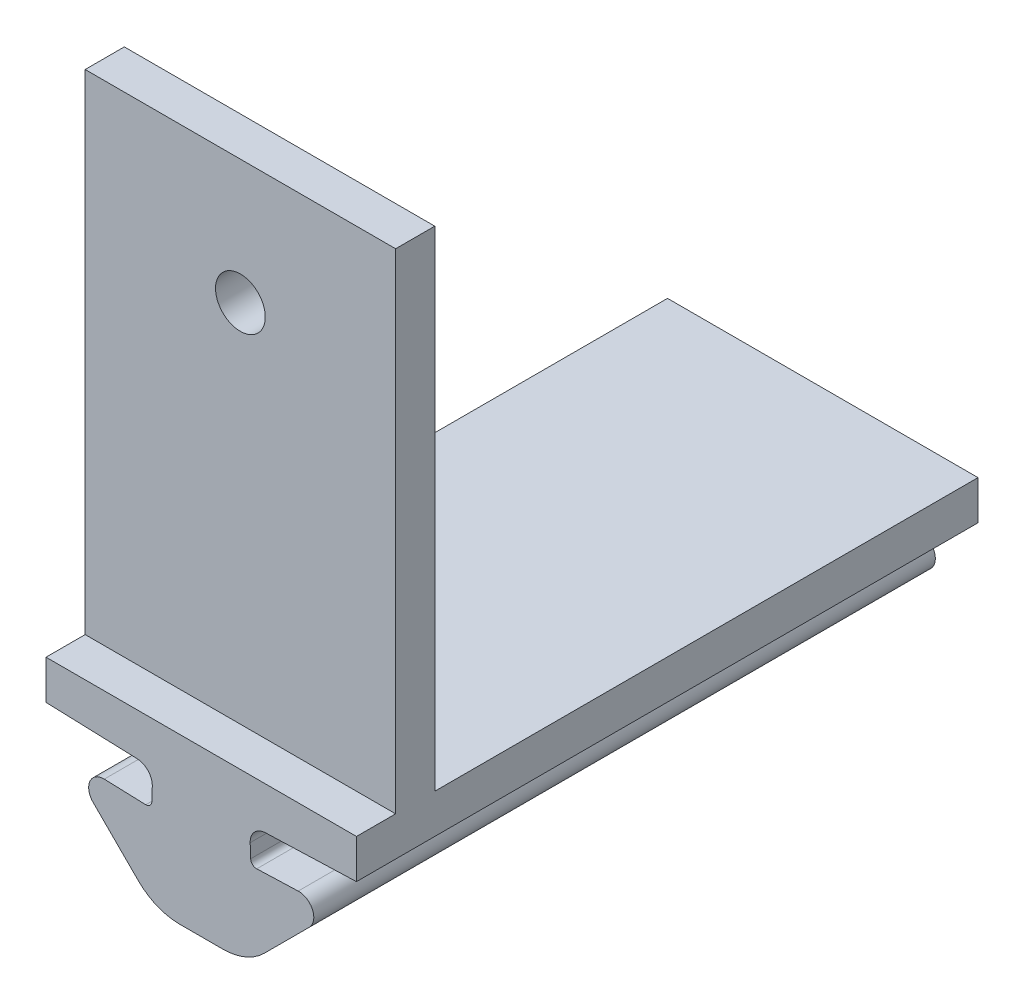
SolidWorks part; units mm, degrees
ref_plane "Front Plane" through (0, 0, 0) normal (0, 0, 1) x (1, 0, 0)
ref_plane "Top Plane" through (0, 0, 0) normal (0, 1, 0) x (1, 0, 0)
ref_plane "Right Plane" through (0, 0, 0) normal (1, 0, 0) x (0, 0, -1)
sketch "Sketch2" plane through (0, 0, 0) normal (0, 0, 1) x (1, 0, 0)
  line L1 (-50.3756, 45.6099) -> (-50.3512, 46.3094)
  line L2 (-50.6859, 45.3205) -> (-52.8037, 45.3945)
  line L6 (-55.7809, 47.2995) -> (-51.1228, 47.1369)
  line L7 (-51.0743, 41.7794) -> (-53.3751, 44.0803)
  line L8 (-47.8507, 40.9008) -> (-48.9529, 40.9008)
  line L9 (-47.8507, 40.9008) -> (-47.8507, 47.2995)
  line L10 (-47.8507, 47.2995) -> (-55.7809, 47.2995)
  arc A0 (-50.6859, 45.3205) -> (-50.3756, 45.6099) centre (-50.6754, 45.6203) ccw
  arc A7 (-50.3512, 46.3094) -> (-51.1228, 47.1369) centre (-51.1507, 46.3374) ccw
  arc A8 (-52.8037, 45.3945) -> (-53.3751, 44.0803) centre (-52.8306, 44.6248) ccw
  arc A9 (-51.0743, 41.7794) -> (-48.9529, 40.9008) centre (-48.9529, 43.9008) ccw
extrude "Boss-Extrude1" add sketch "Sketch2" along normal blind 31.75
ref_plane "Plane2" through (0, 0, 0) normal (0.7071, -0.7071, 0) x (-0.7071, -0.7071, 0)
ref_plane "Plane3" through (-42.746, 42.746, 0) normal (0.7071, -0.7071, 0) x (-0.7071, -0.7071, 0)
mirror "Mirror2" about plane through (-47.8507, 40.9008, 31.75) normal (-1, 0, 0) of "Boss-Extrude1"
ref_plane "Plane7" through (0, 47.2995, 0) normal (0, 1, 0) x (1, 0, 0)
sketch "Sketch19" plane through (0, 47.2995, 0) normal (0, 1, 0) x (1, 0, 0)
  line L0 (-55.7809, -31.75) -> (-55.7809, 0) construction
  line L1 (-55.7809, 0) -> (-39.9205, 0)
  line L2 (-55.7809, 0) -> (-55.7809, -31.75)
  line L3 (-55.7809, -31.75) -> (-39.9205, -31.75)
  line L4 (-39.9205, 0) -> (-39.9205, -31.75)
  line L5 (-39.9205, -31.75) -> (-39.9205, 0) construction
  line L6 (-39.9205, 0) -> (-55.7809, 0) construction
  dimension "D1" = 0
  dimension "D2" = 31.75
extrude "Boss-Extrude7" add sketch "Sketch19" along normal blind 2
sketch "Sketch23" plane through (0, 49.2995, 0) normal (0, 1, 0) x (1, 0, 0)
  line L0 (-55.7809, 0) -> (-55.7809, -31.75) construction
  line L1 (-55.7809, -27.75) -> (-39.9205, -27.75)
  line L2 (-55.7809, -27.75) -> (-55.7809, -29.75)
  line L3 (-55.7809, -29.75) -> (-39.9205, -29.75)
  line L4 (-39.9205, -27.75) -> (-39.9205, -29.75)
  line L5 (-39.9205, -31.75) -> (-39.9205, 0) construction
  line L6 (-39.9205, 0) -> (-55.7809, 0) construction
  dimension "D1" = 2
  dimension "D2" = 0
  dimension "D3" = 0
  dimension "D4" = 29.75
extrude "Boss-Extrude8" add sketch "Sketch23" along normal blind 25
ref_plane "Plane8" through (-39.9205, 49.2995, 27.75) normal (0, -1, 0) x (-1, 0, 0)
sketch "Sketch24" plane through (0, 0, 27.75) normal (0, 0, -1) x (-1, 0, 0)
  line L0 (39.9205, 74.2995) -> (55.7809, 74.2995) construction
  line L2 (47.8507, 74.2995) -> (47.8507, 61.5995) construction
  circle A1 centre (47.8507, 67.9495) radius 1.27
  dimension "D4" = 2.54
  dimension "D5" = 6.35
extrude "Cut-Extrude1" cut sketch "Sketch24" against normal blind 2.54
